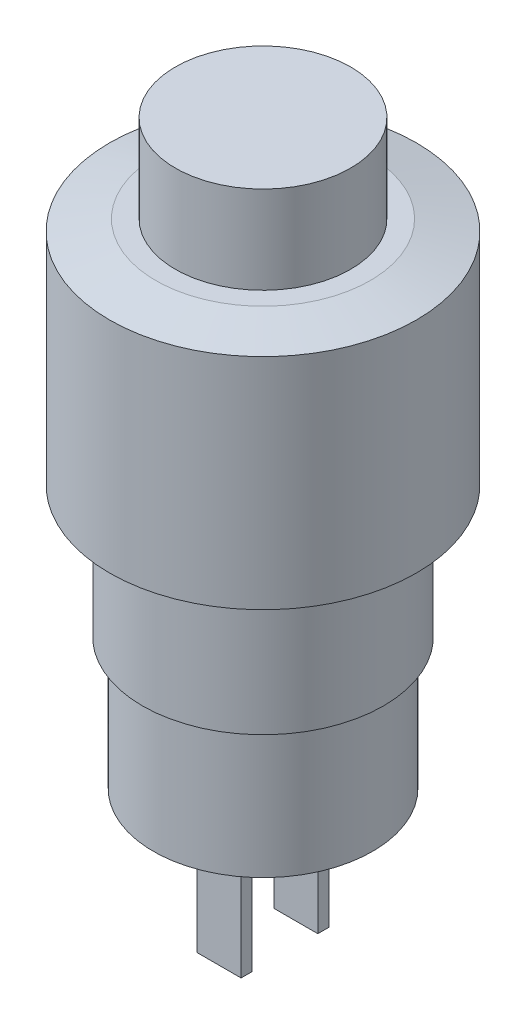
SolidWorks part; units mm, degrees
ref_plane "Plano frontal" through (0, 0, 0) normal (0, 0, 1) x (1, 0, 0)
ref_plane "Plano superior" through (0, 0, 0) normal (0, 1, 0) x (1, 0, 0)
ref_plane "Plano direito" through (0, 0, 0) normal (1, 0, 0) x (0, 0, -1)
sketch "Esboço1" plane through (0, 0, 0) normal (0, 0, 1) x (1, 0, 0)
  line L0 (0, 26.5) -> (4, 26.5)
  line L1 (4, 26.5) -> (4, 22.5)
  line L2 (4, 22.5) -> (4.8913, 22.5)
  line L3 (4.8913, 22.5) -> (7, 22)
  line L4 (7, 22) -> (7, 12)
  line L5 (7, 12) -> (5.5, 12)
  line L6 (5.5, 12) -> (5.5, 6)
  line L7 (5.5, 6) -> (5, 6)
  line L8 (5, 6) -> (5, 0)
  line L11 (5, 0) -> (0, 0)
  line L12 (0, 0) -> (0, 26.5)
  point P2 (0, 0)
  point P12 (3.5, 0)
  point P14 (9, 6)
  point P16 (0, 0)
  point P17 (0, 0)
  point P18 (0, 0)
  dimension "D1" = 6
  dimension "D2" = 5
  dimension "D3" = 6
  dimension "D4" = 0.5
  dimension "D7" = 4
  dimension "D8" = 7
  dimension "D9" = 10.5
  dimension "D10" = 10
  dimension "D11" = 4
revolve "Revolução1" add sketch "Esboço1" angle 360 about L12
sketch "Esboço2" plane through (0, 0, 0) normal (0, -1, 0) x (1, 0, 0)
  line L0 (1.4586, 0) -> (-1.2654, 0) construction
  line L1 (1, -1.5) -> (-1, -1.5)
  line L2 (1, -1.5) -> (1, -2)
  line L3 (1, -2) -> (-1, -2)
  line L4 (-1, -1.5) -> (-1, -2)
  line L5 (1, 2) -> (-1, 2)
  line L6 (-1, 1.5) -> (-1, 2)
  line L7 (1, 1.5) -> (-1, 1.5)
  line L8 (1, 1.5) -> (1, 2)
  point P4 (-1, -1.75)
  point P12 (0, -1.5)
  dimension "D1" = 0.5
  dimension "D2" = 2
  dimension "D3" = 2
extrude "Ressalto-extrusão1" add sketch "Esboço2" along normal blind 6
